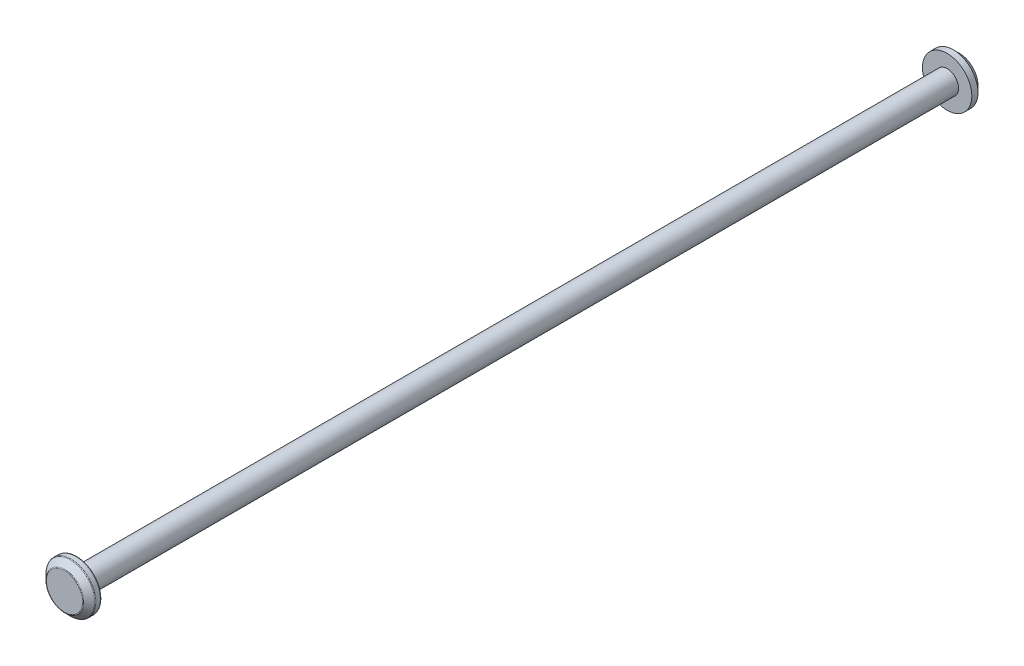
SolidWorks part; units mm, degrees
ref_plane "Front Plane" through (0, 0, 0) normal (0, 0, 1) x (1, 0, 0)
ref_plane "Top Plane" through (0, 0, 0) normal (0, 1, 0) x (1, 0, 0)
ref_plane "Right Plane" through (0, 0, 0) normal (1, 0, 0) x (0, 0, -1)
sketch "Sketch1" plane through (0, 0, 0) normal (0, 0, 1) x (1, 0, 0)
  circle A0 centre (0, 0) radius 0.925
  dimension "D1" = 1.85
extrude "Boss-Extrude1" add sketch "Sketch1" along normal blind 35.25
sketch "Sketch2" plane through (0, 0, 35.25) normal (0, 0, 1) x (1, 0, 0)
  circle A0 centre (0, 0) radius 2
  dimension "D1" = 4
extrude "Boss-Extrude2" add sketch "Sketch2" along normal blind 1
chamfer "Chamfer1" distance 0.5 angle 45 1 edges at (2, 0, 36.25)
mirror "Mirror1" about plane through (0, 0, 0) normal (0, 0, 1) of bodies 102
fillet "Fillet1" radius 0.1 4 edges at (2, 0, 35.25) (0.925, 0, 35.25) (2, 0, 35.75) (1.5, 0, 36.25)
scale "Scale1" scale about centroid uniform scaling yes scale factor 5
